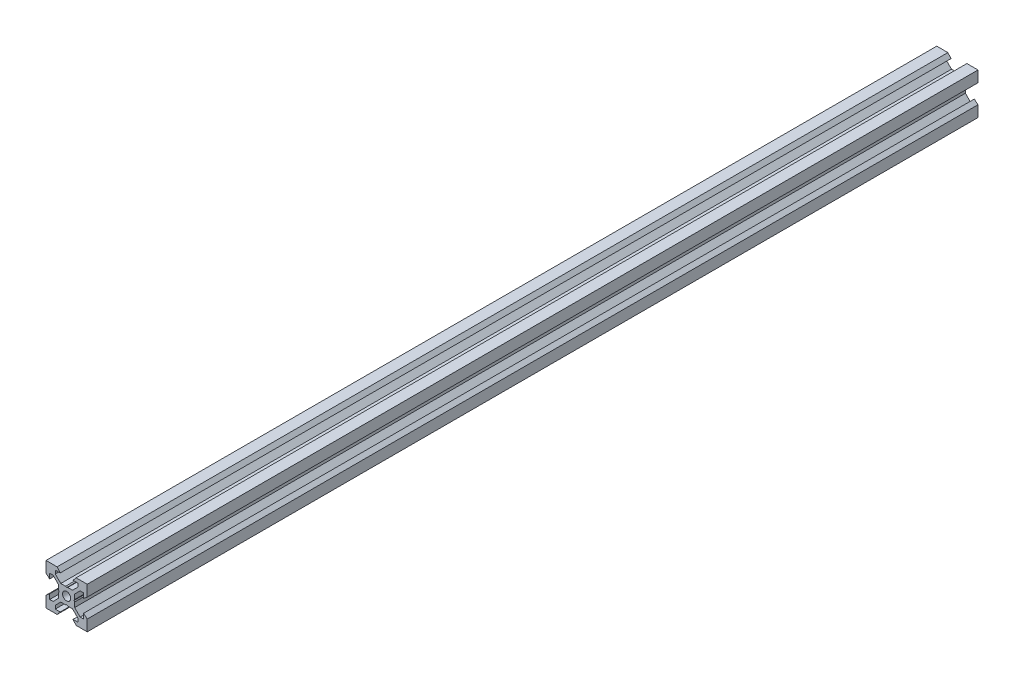
SolidWorks part; units mm, degrees
ref_plane "Front Plane" through (0, 0, 0) normal (0, 0, 1) x (1, 0, 0)
ref_plane "Top Plane" through (0, 0, 0) normal (0, 1, 0) x (1, 0, 0)
ref_plane "Right Plane" through (0, 0, 0) normal (1, 0, 0) x (0, 0, -1)
sketch "Sketch1" plane through (0, 0, 0) normal (0, 0, 1) x (1, 0, 0)
  line L0 (10, 10) -> (4.6104, 10) construction
  line L1 (10, 10) -> (10, 4.6104) construction
  line L2 (10, -10) -> (10, -4.6104) construction
  line L3 (10, -10) -> (4.6104, -10) construction
  line L4 (10, 10) -> (10, 4.6104)
  line L5 (6.5607, 5.5) -> (8.2, 5.5)
  line L6 (5.5, 8.2) -> (5.5, 6.5607)
  line L7 (10, 10) -> (4.6104, 10)
  line L8 (10, 10) -> (10, 4.6104)
  line L9 (6.5607, 5.5) -> (3.9, 2.8393)
  line L10 (5.5, 6.5607) -> (2.8393, 3.9)
  line L11 (10, 4.6104) -> (8.2, 3.1)
  line L12 (4.6104, 10) -> (3.1, 8.2)
  line L13 (8.2, 3.1) -> (8.2, 5.5)
  line L14 (3.1, 8.2) -> (5.5, 8.2)
  line L15 (-6.5607, 5.5) -> (-8.2, 5.5)
  line L16 (6.5607, -5.5) -> (8.2, -5.5)
  line L17 (3.1, -8.2) -> (5.5, -8.2)
  line L18 (8.2, -3.1) -> (8.2, -5.5)
  line L19 (4.6104, -10) -> (3.1, -8.2)
  line L20 (10, -4.6104) -> (8.2, -3.1)
  line L21 (0.5196, -3.9) -> (0, -3.6)
  line L22 (0.5196, 3.9) -> (0, 3.6)
  line L23 (3.6, 0) -> (3.9, -0.5196)
  line L24 (3.9, 0.5196) -> (3.6, 0)
  line L25 (3.9, 0.5196) -> (3.9, 2.8393)
  line L26 (2.8393, 3.9) -> (0.5196, 3.9)
  line L27 (3.9, -2.8393) -> (3.9, -0.5196)
  line L28 (2.8393, -3.9) -> (0.5196, -3.9)
  line L29 (5.5, -6.5607) -> (2.8393, -3.9)
  line L30 (6.5607, -5.5) -> (3.9, -2.8393)
  line L31 (10, -10) -> (10, -4.6104)
  line L32 (10, -10) -> (4.6104, -10)
  line L33 (5.5, -8.2) -> (5.5, -6.5607)
  line L34 (-6.5607, -5.5) -> (-8.2, -5.5)
  line L35 (10, -10) -> (10, -4.6104)
  line L36 (0, 0) -> (0, 8.2) construction
  line L37 (-10, -10) -> (-4.6104, -10) construction
  line L38 (-10, -10) -> (-10, -4.6104) construction
  line L39 (-10, 10) -> (-10, 4.6104) construction
  line L40 (-10, 10) -> (-4.6104, 10) construction
  line L41 (-10, -10) -> (-10, -4.6104)
  line L43 (-5.5, -8.2) -> (-5.5, -6.5607)
  line L44 (-10, -10) -> (-4.6104, -10)
  line L45 (-10, -10) -> (-10, -4.6104)
  line L46 (-6.5607, -5.5) -> (-3.9, -2.8393)
  line L47 (-5.5, -6.5607) -> (-2.8393, -3.9)
  line L48 (-2.8393, -3.9) -> (-0.5196, -3.9)
  line L49 (-3.9, -2.8393) -> (-3.9, -0.5196)
  line L50 (-2.8393, 3.9) -> (-0.5196, 3.9)
  line L51 (-3.9, 0.5196) -> (-3.9, 2.8393)
  line L52 (-3.9, 0.5196) -> (-3.6, 0)
  line L53 (-3.6, 0) -> (-3.9, -0.5196)
  line L54 (-0.5196, 3.9) -> (0, 3.6)
  line L55 (-0.5196, -3.9) -> (0, -3.6)
  line L56 (-10, -4.6104) -> (-8.2, -3.1)
  line L57 (-4.6104, -10) -> (-3.1, -8.2)
  line L58 (-8.2, -3.1) -> (-8.2, -5.5)
  line L59 (-3.1, -8.2) -> (-5.5, -8.2)
  line L60 (-10, -10) -> (10, -10) construction
  line L61 (-10, -10) -> (-10, 10) construction
  line L62 (-3.1, 8.2) -> (-5.5, 8.2)
  line L63 (-8.2, 3.1) -> (-8.2, 5.5)
  line L64 (-4.6104, 10) -> (-3.1, 8.2)
  line L65 (-10, 4.6104) -> (-8.2, 3.1)
  line L66 (-5.5, 6.5607) -> (-2.8393, 3.9)
  line L67 (-6.5607, 5.5) -> (-3.9, 2.8393)
  line L68 (-10, 10) -> (-10, 4.6104)
  line L69 (-10, 10) -> (-4.6104, 10)
  line L70 (-5.5, 8.2) -> (-5.5, 6.5607)
  line L71 (-10, 10) -> (10, 10) construction
  line L72 (-10, 10) -> (-10, 4.6104)
  line L73 (10, -10) -> (10, 10) construction
  line L74 (-10, -10) -> (10, 10) construction
  line L75 (-10, 10) -> (10, -10) construction
  circle A0 centre (0, 0) radius 2
  dimension "D7" = 4
  dimension "D1" = 20
  dimension "D2" = 5.3896
  dimension "D3" = 4.5
  dimension "D4" = 50
  dimension "D5" = 1.8
  dimension "D6" = 1.5104
  dimension "D8" = 5.5
  dimension "D9" = 120
  dimension "D10" = 0.3
  dimension "D11" = 2.3197
  dimension "D12" = 7.8
  dimension "D13" = 7.8
  dimension "D14" = 1.5
  dimension "D15" = 2.6607
extrude "Boss-Extrude1" add sketch "Sketch1" along normal mid plane 432 contours L70 L62 L64 L69 L68 L65 L63 L15 L67 L51 L52 L53 L49 L46 L34 L58 L56 L41 L44 L57 L59 L43 L47 L48 L55 L21 L28 L29 L33 L17 L19 L32 L31 L20 L18 L16 L30 L27 L23 L24 L25 L9 L5 L13 L11 L4 L7 L12 L14 L6 L10
